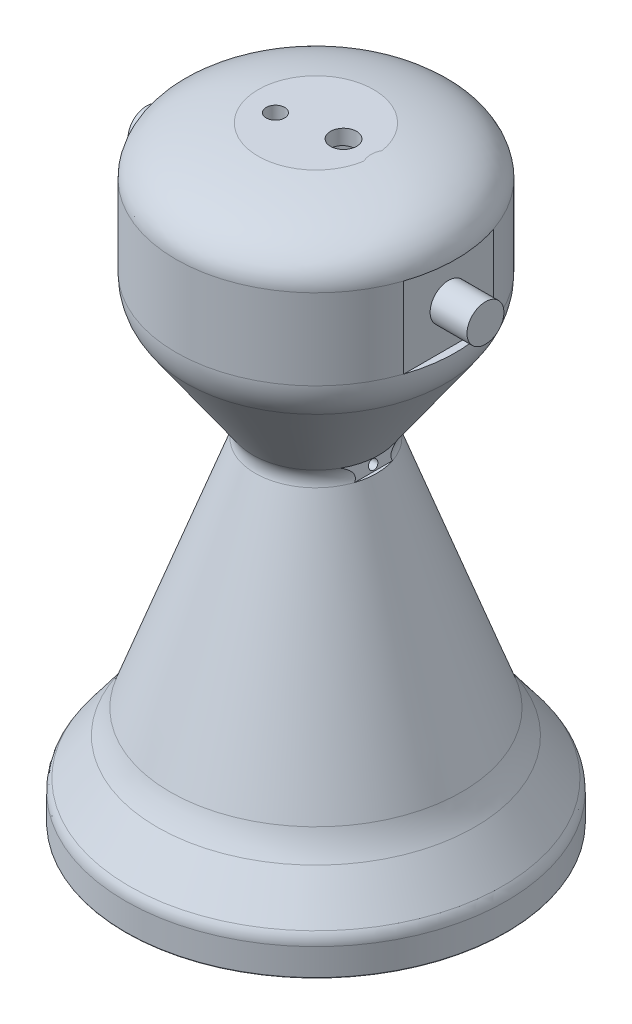
SolidWorks part; units mm, degrees
material "Thornel Mat VMA"
ref_plane "Front Plane" through (0, 0, 0) normal (0, 0, 1) x (1, 0, 0)
ref_plane "Top Plane" through (0, 0, 0) normal (0, 1, 0) x (1, 0, 0)
ref_plane "Right Plane" through (0, 0, 0) normal (1, 0, 0) x (0, 0, -1)
sketch "Sketch1" plane through (0, 0, 0) normal (0, 0, 1) x (1, 0, 0)
  line L0 (23.5609, -9.7835) -> (55.9825, -98.861)
  line L1 (0, 149.9293) -> (0, -123.9696) construction
  line L2 (65.8861, 71.8381) -> (65.8861, 115.5322)
  line L3 (75.8861, 71.8381) -> (75.8861, 115.5322)
  line L4 (34.1632, 2.7927) -> (70.4607, 54.6308)
  line L5 (32.9578, -6.3633) -> (79.0312, -132.9489)
  line L6 (95.7569, -187.051) -> (102.7557, -187.051)
  line L7 (25.9717, 8.5285) -> (62.2692, 60.3666)
  line L8 (103.2557, -186.551) -> (103.2557, -172.0721)
  line L9 (101.242, -166.0539) -> (86.0841, -145.9386)
  line L10 (55.9825, -98.861) -> (95.3005, -186.7552)
  line L11 (0, 133.7467) -> (0, 143.7467)
  line L12 (32.9578, -6.3633) -> (97.801, -184.5183) construction
  line L13 (23.5609, -9.7835) -> (88.404, -187.9385) construction
  arc A0 (65.8861, 71.8381) -> (62.2692, 60.3666) centre (45.8861, 71.8381) cw
  arc A1 (25.9717, 8.5285) -> (23.5609, -9.7835) centre (42.3547, -2.9431) ccw
  arc A2 (75.8861, 71.8381) -> (70.4607, 54.6308) centre (45.8861, 71.8381) cw
  arc A3 (34.1632, 2.7927) -> (32.9578, -6.3633) centre (42.3547, -2.9431) ccw
  arc A4 (103.2557, -172.0721) -> (101.242, -166.0539) centre (93.2557, -172.0721) ccw
  arc A5 (95.3005, -186.7552) -> (95.7569, -187.051) centre (95.7569, -186.551) ccw
  arc A6 (102.7557, -187.051) -> (103.2557, -186.551) centre (102.7557, -186.551) ccw
  arc A7 (79.0312, -132.9489) -> (86.0841, -145.9386) centre (126.0158, -115.8479) ccw
  ellipse E0 centre (0, 115.5322) end of major axis (65.8861, 115.5322) minor radius 18.2146 (65.8861, 115.5322) -> (0, 133.7467) ccw
  spline S0 degree 1 poles (75.8861, 115.5322) (0, 143.7467) knots 0 0 1 1 construction
  spline S1 degree 3 poles (0, 143.7467) (2.2436, 143.7467) (6.7411, 143.6857) (15.6486, 143.3205) (26.4997, 142.4117) (38.63, 140.6226) (49.5053, 138.1618) (57.307, 135.5535) (62.7626, 133.0472) (66.4809, 130.8886) (69.847, 128.3194) (72.8409, 125.0979) (74.8181, 121.5543) (75.7259, 118.2033) (75.8861, 116.4167) (75.8861, 115.5322) knots 0 0 0 0 0.098175 0.19635 0.392699 0.589049 0.785398 0.981748 1.079922 1.178097 1.276272 1.374447 1.472622 1.521709 1.570796 1.570796 1.570796 1.570796
  point P0 (0, 0)
  point P18 (20, 0)
  dimension "D2" = 20
  dimension "D4" = 10
  dimension "D5" = 0.5
  dimension "D6" = 50
  dimension "D1" = 20
  dimension "D3" = 10
revolve "Revolve1" add sketch "Sketch1" angle 360 about L1
sketch "Sketch2" plane through (0, 0, 0) normal (0, 0, 1) x (1, 0, 0)
  line L0 (-31.3141, 141.6627) -> (30.9347, 141.6627)
  line L1 (-31.3141, 141.6627) -> (-13.6948, 150.0331)
  line L2 (-13.6948, 150.0331) -> (30.9347, 141.6627)
  spline S0 degree 3 poles (0, 143.7467) (-2.2436, 143.7467) (-6.7411, 143.6857) (-15.6486, 143.3205) (-26.4997, 142.4117) (-38.63, 140.6226) (-49.5053, 138.1618) (-57.307, 135.5535) (-62.7626, 133.0472) (-66.4809, 130.8886) (-69.847, 128.3194) (-72.8409, 125.0979) (-74.8181, 121.5543) (-75.7259, 118.2033) (-75.8861, 116.4167) (-75.8861, 115.5322) knots 0 0 0 0 0.098175 0.19635 0.392699 0.589049 0.785398 0.981748 1.079922 1.178097 1.276272 1.374447 1.472622 1.521709 1.570796 1.570796 1.570796 1.570796 construction
extrude "Cut-Extrude1" cut sketch "Sketch2" against normal through all and the other way through all
sketch "Sketch3" plane through (0, 141.6627, 0) normal (0, 1, 0) x (1, 0, 0)
  line L0 (0, 0) -> (29.9065, 0) construction
  line L1 (0, 0) -> (-29.1649, -11.4008) construction
  arc A0 (30.9347, 4.86) -> (30.9347, -4.86) centre (0, 0) ccw construction
  circle A1 centre (14.9533, 0) radius 7.0711
  circle A2 centre (-15.7811, -6.169) radius 5
  spline S0 degree 3 poles (30.9347, 4.86) (30.5887, 4.0948) (30.3353, 3.3048) (30.0792, 2.0865) (30.0147, 1.6748) (29.9282, 0.84) (29.9067, 0.4205) (29.9062, -0.8282) (29.9897, -1.6544) (30.2462, -2.8839) (30.3539, -3.2913) (30.6115, -4.0872) (30.7617, -4.4776) (30.9347, -4.86) knots 0 0 0 0 0.25 0.25 0.375 0.375 0.5 0.5 0.75 0.75 0.875 0.875 1 1 1 1 construction
  dimension "D1" = 14.1421
  dimension "D2" = 10
extrude "Cut-Extrude2" cut sketch "Sketch3" against normal up to next
sketch "Sketch4" plane through (0, 0, 0) normal (0, 0, 1) x (1, 0, 0)
  line L0 (34.1632, 2.7927) -> (29.882, 2.7927)
  line L2 (34.1632, 2.7927) -> (-34.1632, 2.7927) construction
  line L3 (32.9578, -6.3633) -> (34.1632, 2.7927)
  line L5 (29.882, 2.7927) -> (31.2991, -6.3633)
  line L6 (32.9578, -6.3633) -> (-32.9578, -6.3633) construction
  line L7 (31.2991, -6.3633) -> (32.9578, -6.3633)
  arc A0 (34.1632, 2.7927) -> (32.9578, -6.3633) centre (42.3547, -2.9431) ccw construction
extrude "Cut-Extrude4" cut sketch "Sketch4" against normal through all and the other way through all
sketch "Sketch5" plane through (29.605, 4.5823, 0) normal (0.9882, 0.153, 0) x (0, 0, -1)
  circle A0 centre (0.1842, -8.0509) radius 2.5
  dimension "D1" = 5
extrude "Cut-Extrude5" cut sketch "Sketch5" against normal up to next
sketch "Sketch7" plane through (0, 0, 0) normal (0, 0, 1) x (1, 0, 0)
  line L0 (75.8861, 115.5322) -> (71.8861, 115.5322)
  line L1 (75.8861, 115.5322) -> (-75.8861, 115.5322) construction
  line L2 (71.8861, 115.5322) -> (71.8861, 71.8381)
  line L3 (75.8861, 71.8381) -> (-75.8861, 71.8381) construction
  line L4 (71.8861, 71.8381) -> (75.8861, 71.8381)
  dimension "D1" = 4
extrude "Cut-Extrude6" cut sketch "Sketch7" against normal through all and the other way through all
sketch "Sketch8" plane through (0, 0, 0) normal (0, 0, 1) x (1, 0, 0)
  line L0 (-75.8861, 115.5322) -> (-71.8861, 115.5322)
  line L1 (-75.8861, 115.5322) -> (71.8861, 115.5322) construction
  line L2 (-71.8861, 115.5322) -> (-71.8861, 71.8381)
  line L3 (-75.8861, 71.8381) -> (71.8861, 71.8381) construction
  line L4 (-71.8861, 71.8381) -> (-75.8861, 71.8381)
  line L5 (-75.8861, 115.5322) -> (-75.8861, 71.8381) construction
  dimension "D1" = 4
extrude "Cut-Extrude8" cut sketch "Sketch8" against normal through all and the other way through all flip side to cut
sketch "Sketch9" plane through (71.8861, 0, 0) normal (1, 0, 0) x (0, 0, -1)
  line L0 (0, 115.5322) -> (0, 71.8381) construction
  line L1 (-24.3123, 115.5322) -> (24.3123, 115.5322) construction
  line L2 (24.3123, 71.8381) -> (-24.3123, 71.8381) construction
  circle A0 centre (0, 93.6852) radius 10
  dimension "D1" = 20
extrude "Boss-Extrude1" add sketch "Sketch9" along normal blind 20
sketch "Sketch10" plane through (-71.8861, 0, 0) normal (-1, 0, 0) x (0, 0, 1)
  line L0 (0, 115.5322) -> (0, 71.8381) construction
  line L1 (-24.3123, 115.5322) -> (24.3123, 115.5322) construction
  line L2 (24.3123, 71.8381) -> (-24.3123, 71.8381) construction
  circle A0 centre (0, 93.6852) radius 10
  dimension "D1" = 20
extrude "Boss-Extrude2" add sketch "Sketch10" along normal blind 20
